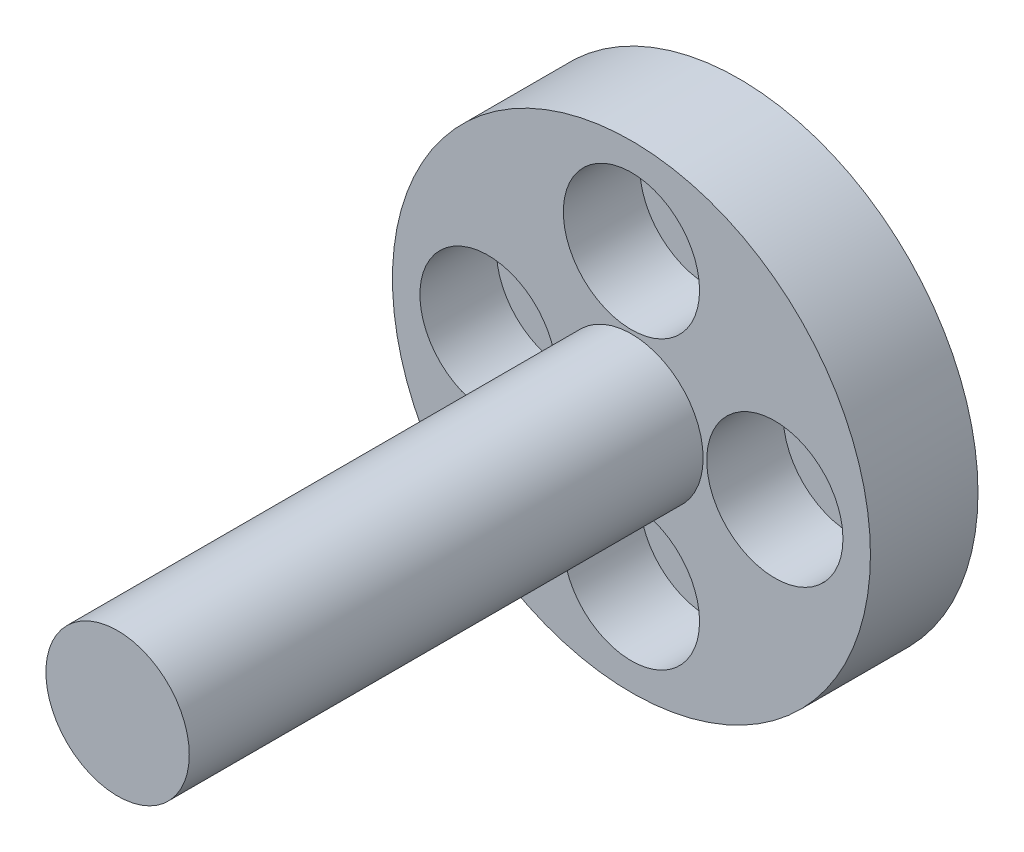
SolidWorks part; units mm, degrees
ref_plane "Front Plane" through (0, 0, 0) normal (0, 0, 1) x (1, 0, 0)
ref_plane "Top Plane" through (0, 0, 0) normal (0, 1, 0) x (1, 0, 0)
ref_plane "Right Plane" through (0, 0, 0) normal (1, 0, 0) x (0, 0, -1)
sketch "Sketch1" plane through (0, 0, 0) normal (0, 0, 1) x (1, 0, 0)
  circle A0 centre (0, 0) radius 10
  dimension "D1" = 20
extrude "Boss-Extrude1" add sketch "Sketch1" along normal blind 4.5
sketch "Sketch2" plane through (0, 0, 4.5) normal (0, 0, 1) x (1, 0, 0)
  circle A0 centre (0, 0) radius 3
  dimension "D1" = 6
extrude "Boss-Extrude2" add sketch "Sketch2" along normal blind 21.5
cosmetic thread "Cosmetic Thread3" parameters "D1"=13.5, "D2"=4.917
sketch "Sketch3" plane through (0, 0, 0) normal (0, 0, -1) x (-1, 0, 0)
  circle A0 centre (0, 0) radius 2
  dimension "D1" = 4
extrude "Cut-Extrude1" cut sketch "Sketch3" against normal blind 6.5
sketch "Sketch4" plane through (0, 0, 0) normal (0, 0, -1) x (-1, 0, 0)
  circle A0 centre (0, 6) radius 1.6
  circle A1 centre (6, 0) radius 1.6
  circle A2 centre (0, -6) radius 1.6
  circle A3 centre (-6, 0) radius 1.6
  point P12 (0, 0)
  dimension "D1" = 3.2
  dimension "D2" = 6
  dimension "D4" = 6
  dimension "D3" = 4
extrude "Cut-Extrude2" cut sketch "Sketch4" against normal through all
sketch "Sketch5" plane through (0, 0, 4.5) normal (0, 0, 1) x (1, 0, 0)
  circle A0 centre (0, 6) radius 1.6 construction
  circle A1 centre (0, 6) radius 1.6 construction
  circle A2 centre (0, 6) radius 2.85
  circle A3 centre (6, 0) radius 2.85
  circle A4 centre (0, -6) radius 2.85
  circle A5 centre (-6, 0) radius 2.85
  point P13 (0, 0)
  dimension "D1" = 5.7
  dimension "D2" = 4
extrude "Cut-Extrude3" cut sketch "Sketch5" against normal blind 3.2
